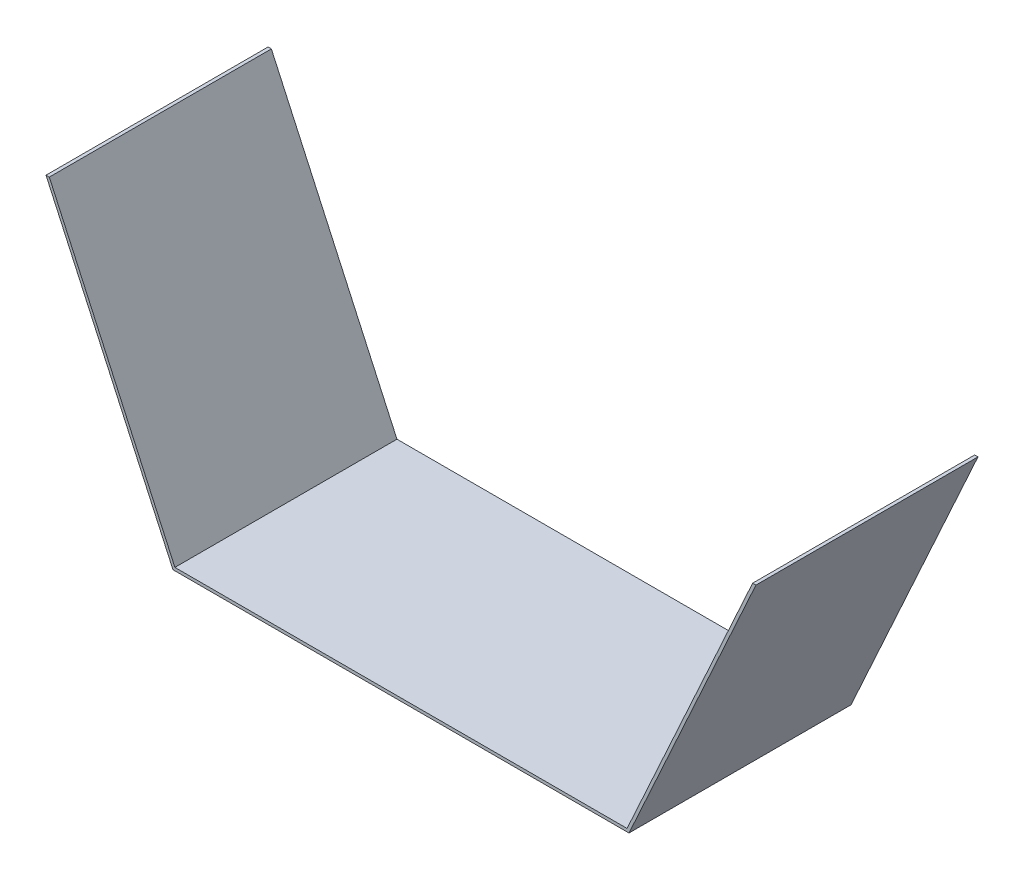
SolidWorks part; units mm, degrees
ref_plane "Front Plane" through (0, 0, 0) normal (0, 0, 1) x (1, 0, 0)
ref_plane "Top Plane" through (0, 0, 0) normal (0, 1, 0) x (1, 0, 0)
ref_plane "Right Plane" through (0, 0, 0) normal (1, 0, 0) x (0, 0, -1)
sketch "Sketch1" plane through (0, 0, 0) normal (0, 0, 1) x (1, 0, 0)
  line L0 (0, -177.8) -> (177.8, -177.8) construction
  line L1 (177.8, -177.8) -> (177.8, 0) construction
  line L2 (-114.3, -177.8) -> (114.3, -177.8)
  line L3 (114.3, -177.8) -> (177.8, -38.6522)
  line L4 (0, -55) -> (0, 55) construction
  line L5 (-114.3, -177.8) -> (-177.8, -38.6522)
  line L6 (-177.8, -38.6522) -> (-179.4696, -38.6522)
  line L7 (-179.4696, -38.6522) -> (-115.2764, -179.3189)
  line L8 (-115.2764, -179.3189) -> (115.2764, -179.3189)
  line L9 (115.2764, -179.3189) -> (179.4696, -38.6522)
  line L10 (179.4696, -38.6522) -> (177.8, -38.6522)
  circle A0 centre (0, 0) radius 177.8 construction
  point P5 (0, 0)
  point P12 (179.3189, -38.6522)
  dimension "D1" = 355.6
  dimension "D2" = 114.3
  dimension "D3" = 1.5189
  dimension "D4" = 1.5189
  dimension "D5" = 1.5189
extrude "Boss-Extrude1" add sketch "Sketch1" along normal blind 112.268
